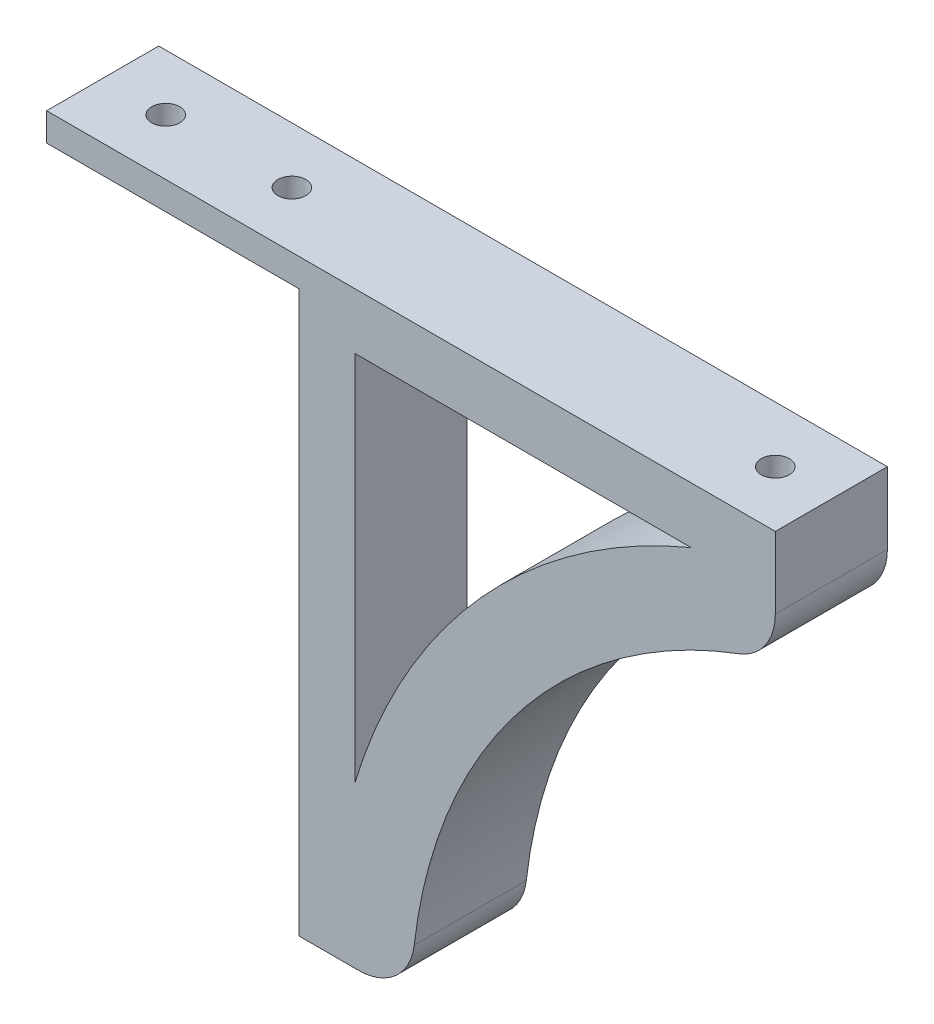
SolidWorks part; units mm, degrees
ref_plane "Plan de face" through (0, 0, 0) normal (0, 0, 1) x (1, 0, 0)
ref_plane "Plan de dessus" through (0, 0, 0) normal (0, 1, 0) x (1, 0, 0)
ref_plane "Plan de droite" through (0, 0, 0) normal (1, 0, 0) x (0, 0, -1)
sketch "Esquisse2" plane through (0, 0, 0) normal (0, 0, 1) x (1, 0, 0)
  line L0 (0, 0) -> (45, 0)
  line L1 (45, 0) -> (45, -100)
  line L2 (45, -100) -> (65, -100)
  line L3 (0, 0) -> (0, 5)
  line L4 (0, 5) -> (130, 5)
  line L5 (130, 5) -> (130, -15)
  line L6 (65, -100) -> (130, -15) construction
  line L8 (55, -100) -> (55, -5) construction
  line L9 (130, -5) -> (55, -100) construction
  line L10 (115, -5) -> (55, -5)
  line L11 (55, -5) -> (55, -71.3576)
  line L12 (130, -5) -> (115, -5) construction
  line L13 (55, -100) -> (55, -71.3576) construction
  arc A0 (130, -15) -> (65, -100) centre (154.9881, -101.4615) ccw
  arc A2 (115, -5) -> (55, -71.3576) centre (154.9881, -101.4615) ccw
  dimension "D1" = 45
  dimension "D2" = 100
  dimension "D3" = 20
  dimension "D4" = 20
  dimension "D5" = 130
  dimension "D6" = 60
  dimension "D7" = 15
extrude "Boss.-Extru.1" add sketch "Esquisse2" along normal blind 20
fillet "Congé1" radius 10 1 edges at (130, -15, 10)
fillet "Congé2" radius 10 1 edges at (65, -100, 10)
sketch "Esquisse3" plane through (0, 0, 0) normal (0, -1, 0) x (1, 0, 0)
  line L1 (45, 20) -> (45, 0) construction
  line L2 (0, 20) -> (45, 20) construction
  line L3 (45, 20) -> (45, 0) construction
  circle A1 centre (33.75, 10) radius 2.5
  circle A2 centre (11.25, 10) radius 2.5
extrude "Enlèv. mat.-Extru.1" cut sketch "Esquisse3" against normal blind 20
sketch "Esquisse4" plane through (0, 5, 0) normal (0, 1, 0) x (1, 0, 0)
  line L0 (130, -20) -> (110, -20) construction
  line L1 (130, -20) -> (0, -20) construction
  line L2 (110, -20) -> (110, 0) construction
  line L3 (130, 0) -> (0, 0) construction
  line L4 (110, 0) -> (130, -20) construction
  line L5 (130, -20) -> (130, 0) construction
  line L6 (130, 0) -> (110, -20) construction
  circle A0 centre (120, -10) radius 2.5
extrude "Enlèv. mat.-Extru.2" cut sketch "Esquisse4" against normal through all
ref_plane "Plan2" through (0, -17.19, 0) normal (0, 1, 0) x (1, 0, 0)
sketch "Esquisse5" plane through (0, -17.19, 0) normal (0, 1, 0) x (1, 0, 0)
  line L0 (120, -10) -> (120, -20.5955) construction
  circle A0 centre (120, -10) radius 4.2
extrude "Enlèv. mat.-Extru.3" cut sketch "Esquisse5" along normal blind 3 and the other way blind 13
